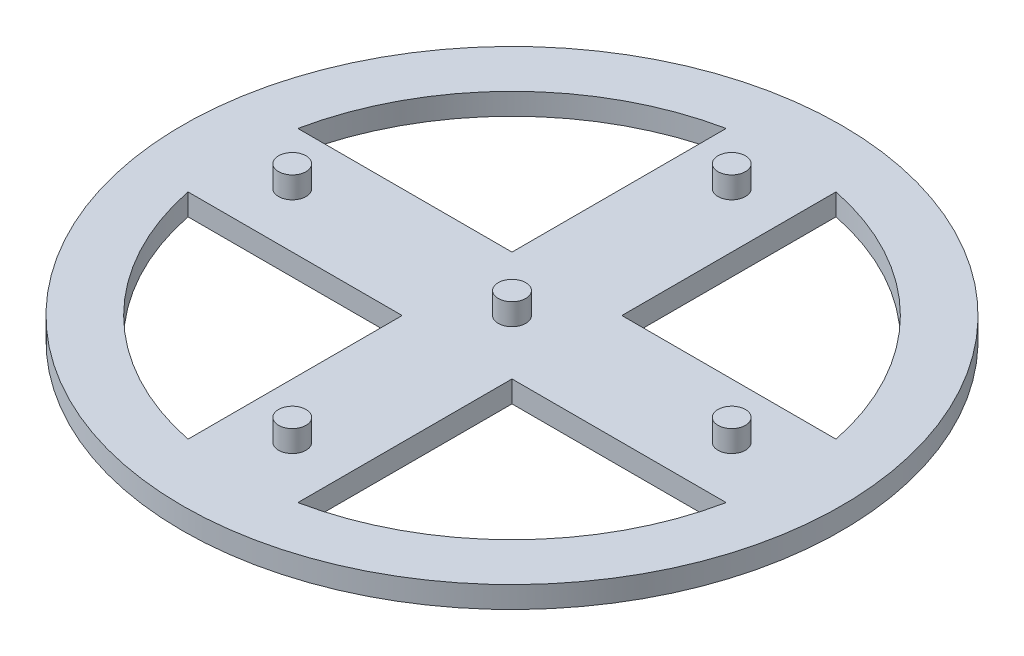
SolidWorks part; units mm, degrees
ref_plane "Front Plane" through (0, 0, 0) normal (0, 0, 1) x (1, 0, 0)
ref_plane "Top Plane" through (0, 0, 0) normal (0, 1, 0) x (1, 0, 0)
ref_plane "Right Plane" through (0, 0, 0) normal (1, 0, 0) x (0, 0, -1)
sketch "Sketch1" plane through (0, 0, 0) normal (0, 1, 0) x (1, 0, 0)
  line L0 (-6.35, 31.1085) -> (-6.35, 6.35)
  line L1 (6.35, 6.35) -> (31.1085, 6.35)
  line L2 (6.35, -31.1085) -> (6.35, -6.35)
  line L3 (-31.1085, 6.35) -> (-6.35, 6.35)
  line L4 (-6.35, -6.35) -> (-6.35, -31.1085)
  line L5 (31.1085, -6.35) -> (6.35, -6.35)
  line L6 (-6.35, -6.35) -> (-31.1085, -6.35)
  line L7 (6.35, 6.35) -> (6.35, 31.1085)
  circle A0 centre (0, 0) radius 38.1
  arc A1 (31.1085, 6.35) -> (6.35, 31.1085) centre (0, 0) ccw
  arc A2 (-6.35, 31.1085) -> (-31.1085, 6.35) centre (0, 0) ccw
  arc A3 (-31.1085, -6.35) -> (-6.35, -31.1085) centre (0, 0) ccw
  arc A4 (6.35, -31.1085) -> (31.1085, -6.35) centre (0, 0) ccw
  dimension "D1" = 76.2
  dimension "D2" = 31.75
  dimension "D3" = 12.7
  dimension "D4" = 6.35
  dimension "D5" = 12.7
  dimension "D6" = 6.35
extrude "Boss-Extrude1" add sketch "Sketch1" along normal blind 2.5 contours A0 A4 L2 L5 A3 L6 L4 A2 L0 L3 A1 L1 L7
sketch "Sketch2" plane through (0, 2.5, 0) normal (0, 1, 0) x (1, 0, 0)
  circle A0 centre (0, 0) radius 1.5875
  circle A1 centre (-25.4, 0) radius 1.5875
  circle A2 centre (0, 25.4) radius 1.5875
  circle A3 centre (25.4, 0) radius 1.5875
  circle A4 centre (0, -25.4) radius 1.5875
  dimension "D1" = 3.175
  dimension "D2" = 50.8
  dimension "D3" = 50.8
  dimension "D4" = 25.4
  dimension "D5" = 25.4
extrude "Boss-Extrude2" add sketch "Sketch2" along normal blind 2.5
